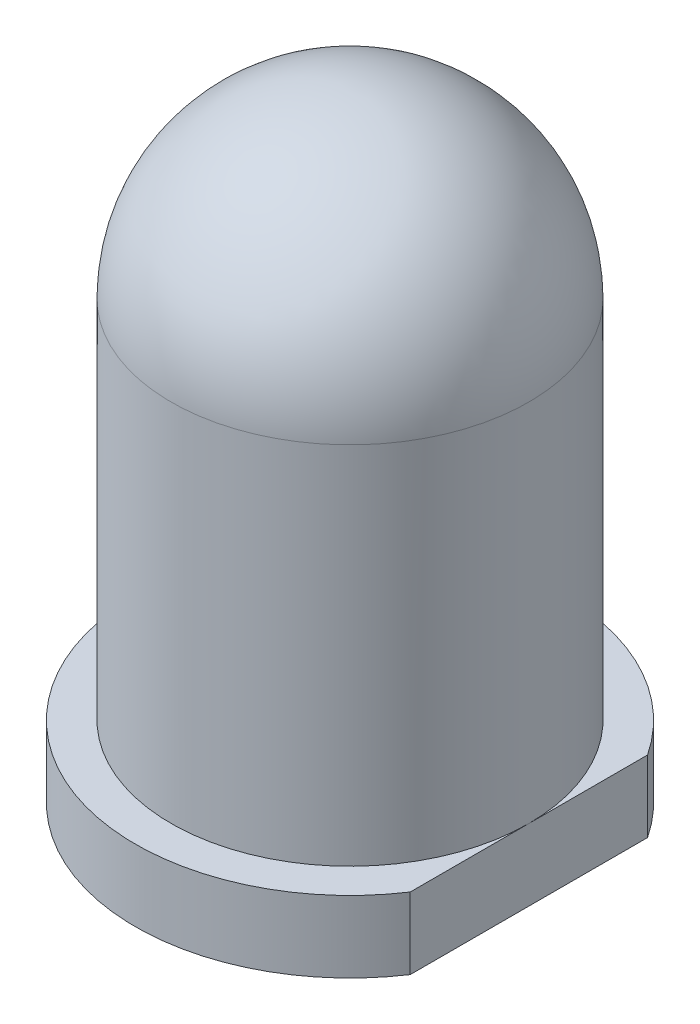
SolidWorks part; units mm, degrees
material "uhlíková ocel 7850"
ref_plane "Přední rovina" through (0, 0, 0) normal (0, 0, 1) x (1, 0, 0)
ref_plane "Horní rovina" through (0, 0, 0) normal (0, 1, 0) x (1, 0, 0)
ref_plane "Pravá rovina" through (0, 0, 0) normal (1, 0, 0) x (0, 0, -1)
sketch "Skica1" plane through (0, 0, 0) normal (0, 0, 1) x (1, 0, 0)
  line L0 (0, 0) -> (0, 8.6) construction
  line L1 (0, 0) -> (-3, 0)
  line L2 (-3, 0) -> (-3, 1)
  line L3 (-3, 1) -> (-2.5, 1)
  line L4 (-2.5, 1) -> (-2.5, 6.1)
  line L5 (0, 0) -> (0, 8.6)
  arc A0 (-2.5, 6.1) -> (0, 8.6) centre (0, 6.1) cw
  dimension "D5" = 2.5
  dimension "D1" = 6
  dimension "D2" = 5
  dimension "D3" = 1
  dimension "D4" = 8.6
revolve "Rotovat1" add sketch "Skica1" angle 360 about L0
sketch "Skica2" plane through (0, 0, 0) normal (0, 1, 0) x (1, 0, 0)
  line L1 (2.5, 2.7252) -> (3.4054, 2.7252)
  line L2 (2.5, 2.7252) -> (2.5, -3.0587)
  line L3 (2.5, -3.0587) -> (3.4054, -3.0587)
  line L4 (3.4054, 2.7252) -> (3.4054, -3.0587)
  circle A0 centre (0, 0) radius 2.5 construction
extrude "Odebrat vysunutím2" cut sketch "Skica2" along normal blind 10
